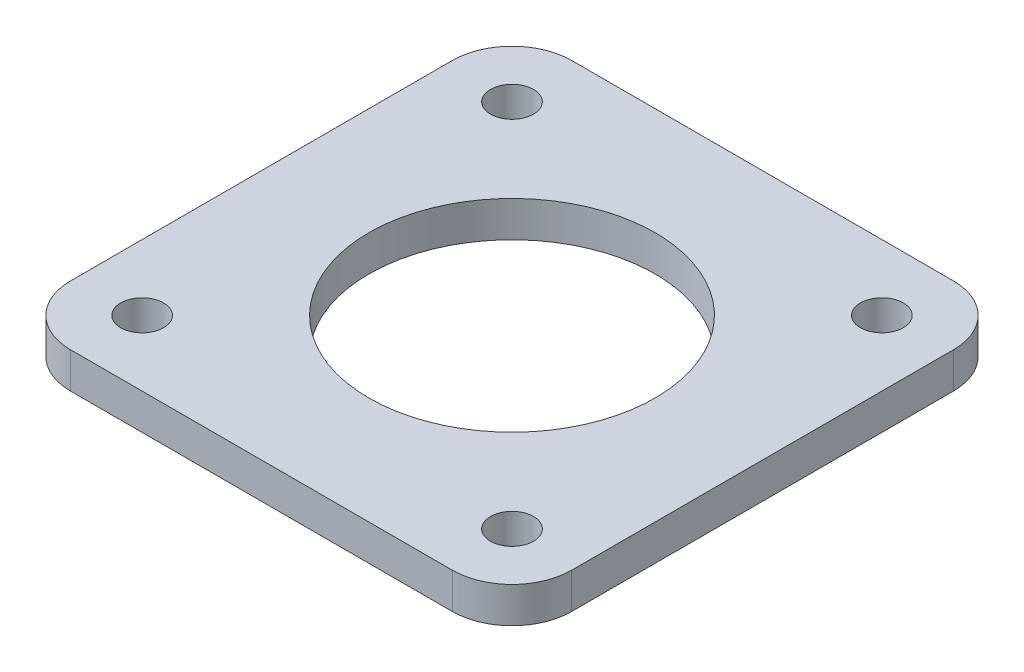
SolidWorks part; units mm, degrees
ref_plane "Front Plane" through (0, 0, 0) normal (0, 0, 1) x (1, 0, 0)
ref_plane "Top Plane" through (0, 0, 0) normal (0, 1, 0) x (1, 0, 0)
ref_plane "Right Plane" through (0, 0, 0) normal (1, 0, 0) x (0, 0, -1)
sketch "Sketch1" plane through (0, 0, 0) normal (0, 1, 0) x (1, 0, 0)
  line L1 (21, 21) -> (-21, 21)
  line L2 (21, 21) -> (21, -21)
  line L3 (21, -21) -> (-21, -21)
  line L4 (-21, 21) -> (-21, -21)
  line L5 (0, -21) -> (0, 21) construction
  line L6 (21, 0) -> (-21, 0) construction
  line L7 (15.5, 15.5) -> (-15.5, 15.5) construction
  line L8 (15.5, 15.5) -> (15.5, -15.5) construction
  line L9 (15.5, -15.5) -> (-15.5, -15.5) construction
  line L10 (-15.5, 15.5) -> (-15.5, -15.5) construction
  line L11 (0, -15.5) -> (0, 15.5) construction
  line L12 (15.5, 0) -> (-15.5, 0) construction
  point P0 (0, 0)
  point P4 (0, 0)
  dimension "D1" = 31
  dimension "D2" = 31
  dimension "D3" = 42
extrude "Boss-Extrude1" add sketch "Sketch1" along normal blind 3
hole_wizard "M3 Clearance Hole1" positions "Sketch2" profile "Sketch3" hole size "M3" standard "ANSI Metric" end condition through all
sketch "Sketch2" plane through (0, 3, 0) normal (0, 1, 0) x (1, 0, 0)
  point P0 (-15.5, 15.5)
  point P3 (-15.5, -15.5)
  point P6 (15.5, -15.5)
  point P9 (15.5, 15.5)
sketch "Sketch3" plane through (-15.5, 3, -15.5) normal (1, 0, 0) x (0, 0, 1)
  line L0 (0, 0) -> (0, 3)
  line L1 (0, 3) -> (1.8, 3)
  line L2 (1.8, 3) -> (1.8, 0)
  line L5 (1.8, 0) -> (0, 0)
  line L11 (0, -6.35) -> (0, 107.95) construction
  dimension "Thru Hole Dia." = 3.6
  dimension "Thru Hole Depth" = 3
sketch "Sketch4" plane through (0, 3, 0) normal (0, 1, 0) x (1, 0, 0)
  line L0 (21, 0) -> (-21, 0) construction
  circle A0 centre (0, 0) radius 12
  dimension "D1" = 24
extrude "Cut-Extrude1" cut sketch "Sketch4" against normal through all
fillet "Fillet1" radius 5 4 edges at (-21, 1.5, -21) (21, 1.5, -21) (21, 1.5, 21) (-21, 1.5, 21)
